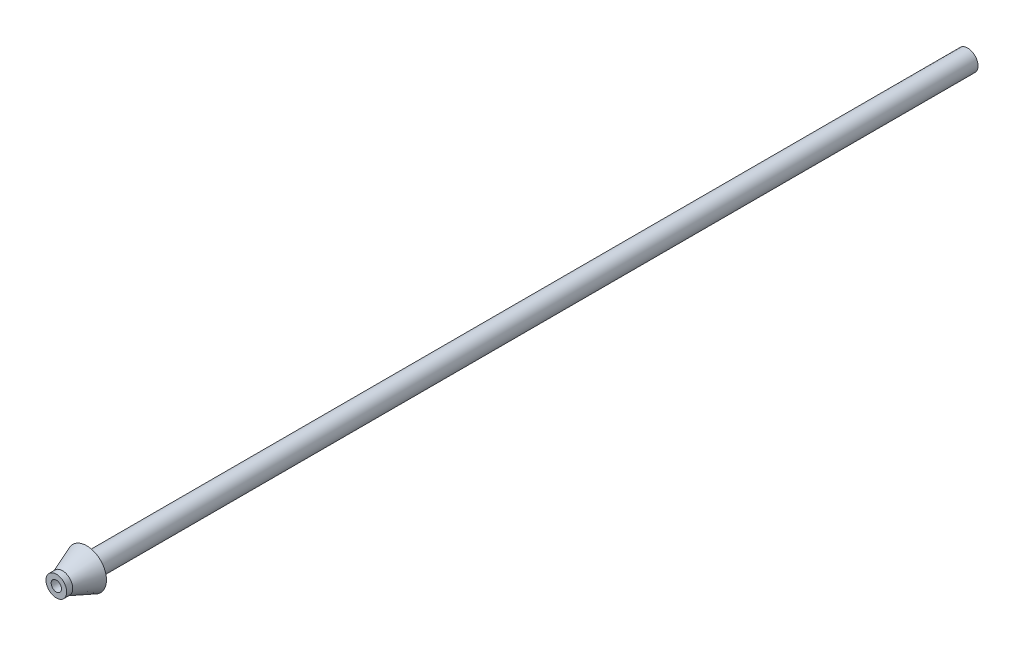
SolidWorks part; units mm, degrees
material "AISI 316 Annealed Stainless Steel Bar (SS)"
ref_plane "Front Plane" through (0, 0, 0) normal (0, 0, 1) x (1, 0, 0)
ref_plane "Top Plane" through (0, 0, 0) normal (0, 1, 0) x (1, 0, 0)
ref_plane "Right Plane" through (0, 0, 0) normal (1, 0, 0) x (0, 0, -1)
sketch "Sketch1" plane through (0, 0, 0) normal (0, 0, 1) x (1, 0, 0)
  circle A0 centre (0, 0) radius 1.7
  circle A1 centre (0, 0) radius 0.85
  dimension "D1" = 3.4
  dimension "D2" = 1.7
extrude "Boss-Extrude1" add sketch "Sketch1" along normal blind 150
sketch "Sketch3" plane through (0, 0, 0) normal (1, 0, 0) x (0, 0, -1)
  line L1 (0, 1.7) -> (-150, 1.7) construction
  line L2 (-149, 1.7) -> (-145, 3.25)
  line L3 (-145, 3.25) -> (-145, 1.7)
  line L4 (1.87, 0) -> (-1.87, 0) construction
  line L5 (-149, 1.7) -> (-145, 1.7)
  dimension "D1" = 4
  dimension "D2" = 3.25
ref_axis "Axis1" through (0, 0, 150) along (0, 0, -1)
revolve "Revolve1" add sketch "Sketch3" angle 360 about axis through (0, 0, 150) along (0, 0, -1)
